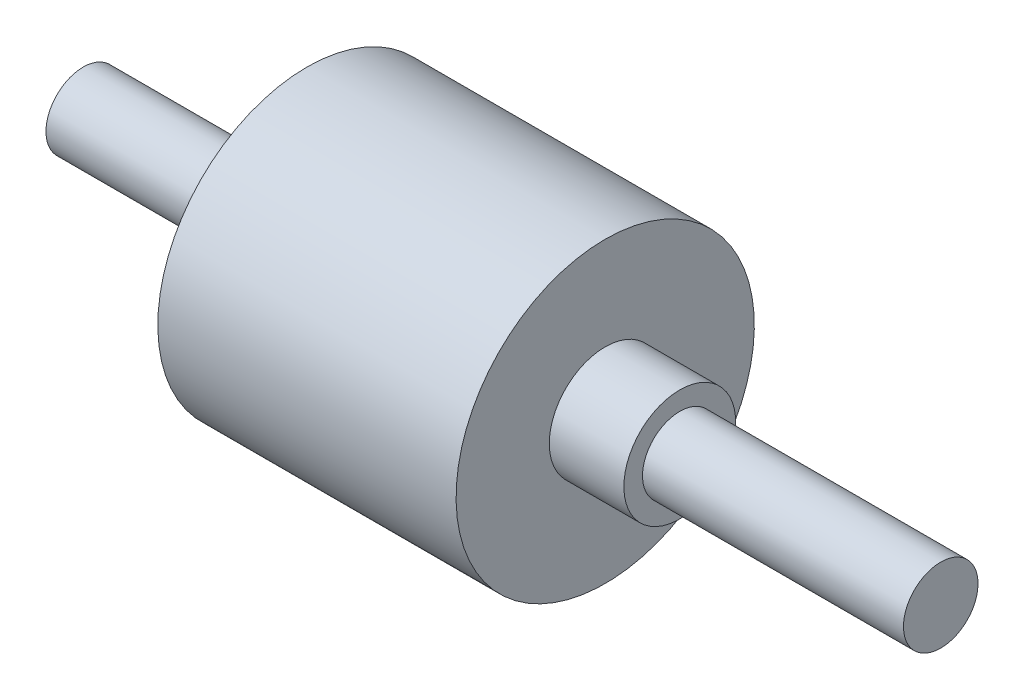
SolidWorks part; units mm, degrees
ref_plane "Front Plane" through (0, 0, 0) normal (0, 0, 1) x (1, 0, 0)
ref_plane "Top Plane" through (0, 0, 0) normal (0, 1, 0) x (1, 0, 0)
ref_plane "Right Plane" through (0, 0, 0) normal (1, 0, 0) x (0, 0, -1)
sketch "Sketch1" plane through (0, 0, 0) normal (0, 0, 1) x (1, 0, 0)
  line L0 (57.5, 0) -> (-57.5, 0)
  line L1 (-57.5, 0) -> (-57.5, 5)
  line L2 (-57.5, 5) -> (-27.5, 5)
  line L3 (-27.5, 5) -> (-27.5, 20)
  line L4 (-27.5, 20) -> (12.5, 20)
  line L5 (12.5, 20) -> (12.5, 7.5)
  line L6 (12.5, 7.5) -> (22.5, 7.5)
  line L7 (22.5, 7.5) -> (22.5, 5)
  line L8 (22.5, 5) -> (57.5, 5)
  line L9 (57.5, 5) -> (57.5, 0)
  point P2 (-57.5, 2.5)
  dimension "D1" = 30
  dimension "D2" = 40
  dimension "D3" = 10
  dimension "D4" = 115
  dimension "D5" = 5
  dimension "D6" = 2.5
  dimension "D7" = 15
  dimension "D8" = 57.5
revolve "Revolve2" add sketch "Sketch1" angle 360 about L0
